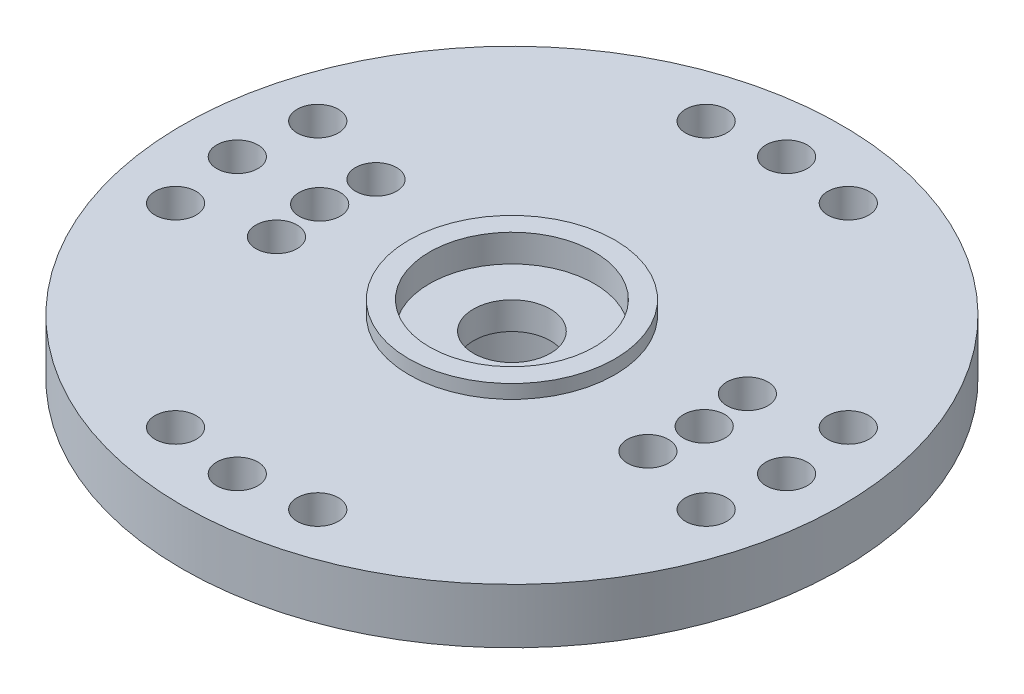
SolidWorks part; units mm, degrees
material "PC High Viscosity"
ref_plane "Front Plane" through (0, 0, 0) normal (0, 0, 1) x (1, 0, 0)
ref_plane "Top Plane" through (0, 0, 0) normal (0, 1, 0) x (1, 0, 0)
ref_plane "Right Plane" through (0, 0, 0) normal (1, 0, 0) x (0, 0, -1)
sketch "Sketch1" plane through (0, 0, 0) normal (0, 0, 1) x (1, 0, 0)
  line L0 (0, 0) -> (0, -4.5) construction
  line L1 (0, -55) -> (0, 55) construction
  line L2 (55, 0) -> (-55, 0) construction
  line L3 (-12, 0) -> (-3.75, 0)
  line L4 (-12, 0) -> (-12, -2)
  line L5 (-12, -2) -> (-4.45, -2)
  line L6 (-1.4, 0.5) -> (-1.4, -4.5)
  line L8 (-4.45, -2) -> (-4.45, -4.5)
  line L9 (-4.45, -4.5) -> (-1.4, -4.5)
  line L10 (-3.75, 0.5) -> (-1.4, 0.5)
  line L11 (-3.75, 0.5) -> (-3.75, 0)
  dimension "D1" = 8.9
  dimension "D2" = 2.5
  dimension "D3" = 4.5
  dimension "D4" = 24
  dimension "D5" = 2.8
  dimension "D6" = 7.5
  dimension "D7" = 5
revolve "Revolve1" add sketch "Sketch1" angle 360 about L0
hole_wizard "Ø1.5 (1.5) Diameter Hole1" positions "Sketch3" profile "Sketch2" hole size "Ø1.5" standard "Ansi Metric" end condition up to next
sketch "Sketch3" plane through (0, 0, 0) normal (0, 1, 0) x (-1, 0, 0)
  line L5 (0, 0) -> (-2.5882, -9.6593) construction
  line L6 (0, 0) -> (2.5882, -9.6593) construction
  line L8 (0, 0) -> (0, -10) construction
  circle A0 centre (0, 0) radius 10 construction
  point P0 (0, -10)
  point P23 (2.5882, -9.6593)
  point P25 (-2.5882, -9.6593)
  dimension "D1" = 20
  dimension "D2" = 15
  dimension "D3" = 15
sketch "Sketch2" plane through (0, 0, -10) normal (1, 0, 0) x (0, 0, 1)
  line L0 (0, 0) -> (0, 2)
  line L1 (0, 2) -> (0.75, 2)
  line L2 (0.75, 2) -> (0.75, 0)
  line L5 (0.75, 0) -> (0, 0)
  line L11 (0, -6.35) -> (0, 107.95) construction
  dimension "Thru Hole Dia." = 1.5
  dimension "Thru Hole Depth" = 2
pattern_circular "CirPattern1" count 4 over 360 about axis through (0, 0, 0) along (0, 1, 0) of "Ø1.5 (1.5) Diameter Hole1"
sketch "Sketch4" plane through (0, 0.5, 0) normal (0, 1, 0) x (-1, 0, 0)
  circle A0 centre (0, 0) radius 3
  dimension "D1" = 6
extrude "Cut-Extrude1" cut sketch "Sketch4" against normal blind 1
sketch "Sketch5" plane through (0, -4.5, 0) normal (0, -1, 0) x (1, 0, 0)
  circle A0 centre (0, 0) radius 3
  dimension "D1" = 6
extrude "Cut-Extrude2" cut sketch "Sketch5" against normal blind 3
hole_wizard "Ø1.5 (1.5) Diameter Hole2" positions "Sketch7" profile "Sketch6" hole size "Ø1.5" standard "Ansi Metric" end condition up to next
sketch "Sketch7" plane through (0, 0, 0) normal (0, 1, 0) x (-1, 0, 0)
  line L0 (7, 0) -> (0, 0) construction
  line L1 (0, 0) -> (6.7615, 1.8117) construction
  line L2 (0, 0) -> (6.7615, -1.8117) construction
  circle A0 centre (0, 0) radius 7 construction
  point P0 (6.7615, -1.8117)
  point P1 (7, 0)
  point P3 (6.7615, 1.8117)
  dimension "D3" = 14
  dimension "D1" = 15
  dimension "D2" = 15
sketch "Sketch6" plane through (-6.7615, 0, -1.8117) normal (1, 0, 0) x (0, 0, 1)
  line L0 (0, 0) -> (0, 2)
  line L1 (0, 2) -> (0.75, 2)
  line L2 (0.75, 2) -> (0.75, 0)
  line L5 (0.75, 0) -> (0, 0)
  line L11 (0, -6.35) -> (0, 107.95) construction
  dimension "Thru Hole Dia." = 1.5
  dimension "Thru Hole Depth" = 2
pattern_circular "CirPattern2" count 2 over 360 about axis through (0, 0, 0) along (0, 1, 0) of "Ø1.5 (1.5) Diameter Hole2"
